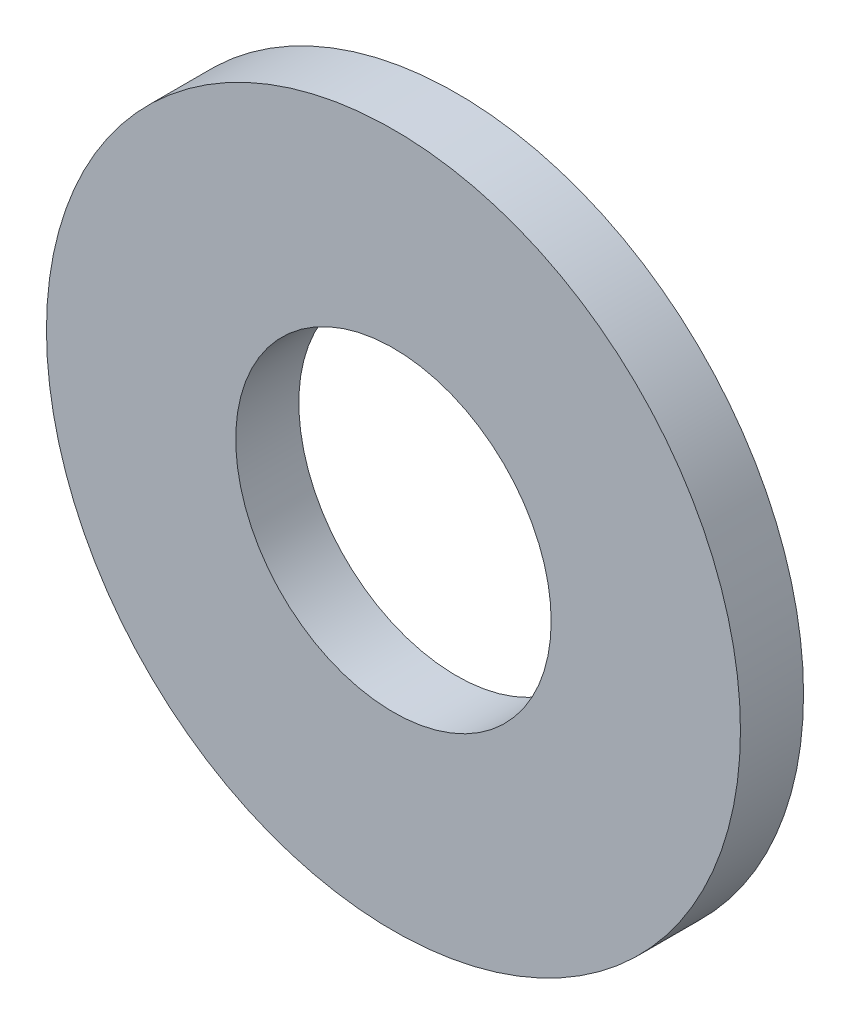
SolidWorks part; units mm, degrees
material "3.0255 (EN-AW 1350A)"
ref_plane "Plan de face" through (0, 0, 0) normal (0, 0, 1) x (1, 0, 0)
ref_plane "Plan de dessus" through (0, 0, 0) normal (0, 1, 0) x (1, 0, 0)
ref_plane "Plan de droite" through (0, 0, 0) normal (1, 0, 0) x (0, 0, -1)
sketch "Esquisse1" plane through (0, 0, 0) normal (0, 0, 1) x (1, 0, 0)
  circle A0 centre (0, 0) radius 5
  circle A1 centre (0, 0) radius 11
  dimension "D1" = 10
  dimension "D2" = 22
extrude "Boss.-Extru.1" add sketch "Esquisse1" along normal blind 2
